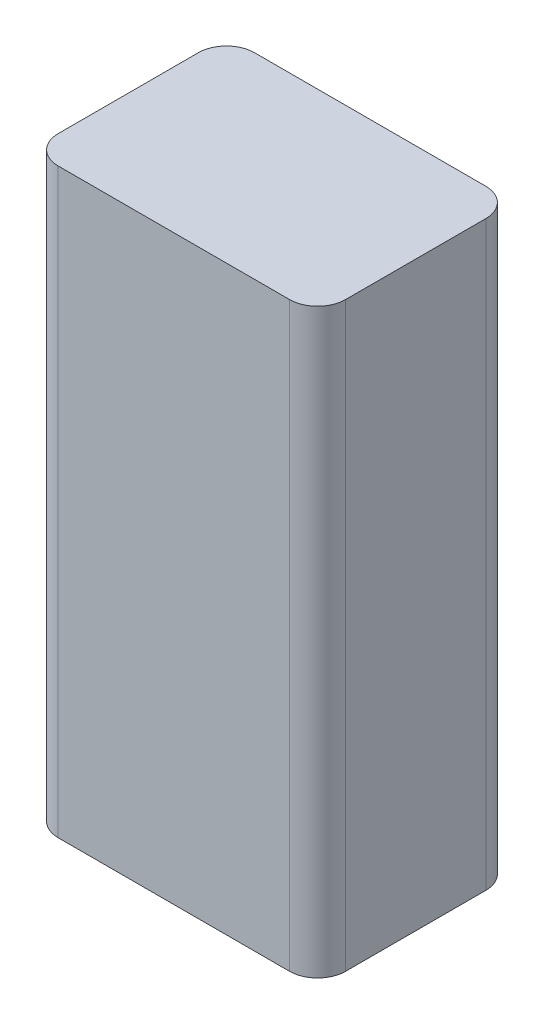
SolidWorks part; units mm, degrees
ref_plane "Front Plane" through (0, 0, 0) normal (0, 0, 1) x (1, 0, 0)
ref_plane "Top Plane" through (0, 0, 0) normal (0, 1, 0) x (1, 0, 0)
ref_plane "Right Plane" through (0, 0, 0) normal (1, 0, 0) x (0, 0, -1)
sketch "Sketch1" plane through (0, 0, 0) normal (0, 0, 1) x (1, 0, 0)
  line L1 (0, 0) -> (26.035, 0)
  line L2 (0, 0) -> (0, -52.705)
  line L3 (0, -52.705) -> (26.035, -52.705)
  line L4 (26.035, 0) -> (26.035, -52.705)
  dimension "D1" = 52.705
  dimension "D2" = 26.035
extrude "Boss-Extrude1" add sketch "Sketch1" along normal blind 17.78
fillet "Fillet1" radius 2.54 4 edges at (0, -26.3525, 0) (26.035, -26.3525, 0) (26.035, -26.3525, 17.78) (0, -26.3525, 17.78)
